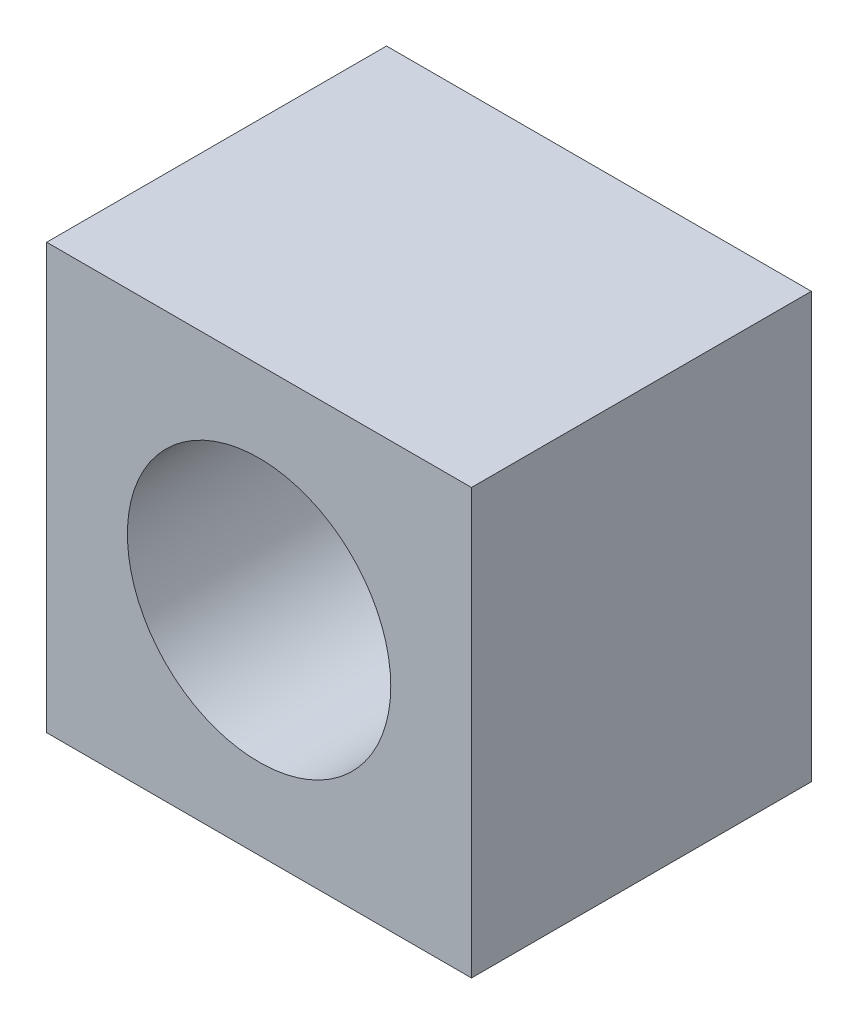
SolidWorks part; units mm, degrees
ref_plane "Front Plane" through (0, 0, 0) normal (0, 0, 1) x (1, 0, 0)
ref_plane "Top Plane" through (0, 0, 0) normal (0, 1, 0) x (1, 0, 0)
ref_plane "Right Plane" through (0, 0, 0) normal (1, 0, 0) x (0, 0, -1)
sketch "Sketch1" plane through (0, 0, 0) normal (0, 0, 1) x (1, 0, 0)
  line L1 (-5, -5) -> (5, -5)
  line L2 (-5, -5) -> (-5, 5)
  line L3 (-5, 5) -> (5, 5)
  line L4 (5, -5) -> (5, 5)
  line L5 (-5, -5) -> (5, 5) construction
  line L6 (-5, 5) -> (5, -5) construction
  circle A0 centre (0, 0) radius 1.25
  point P0 (0, 0)
  dimension "D3" = 2.5
  dimension "D1" = 10
  dimension "D2" = 10
extrude "Main" add sketch "Sketch1" along normal blind 8
sketch "Sketch2" plane through (0, 0, 8) normal (0, 0, 1) x (1, 0, 0)
  circle A0 centre (0, 0) radius 3.1
  dimension "D1" = 6.2
extrude "Cut-Extrude1" cut sketch "Sketch2" against normal blind 5
